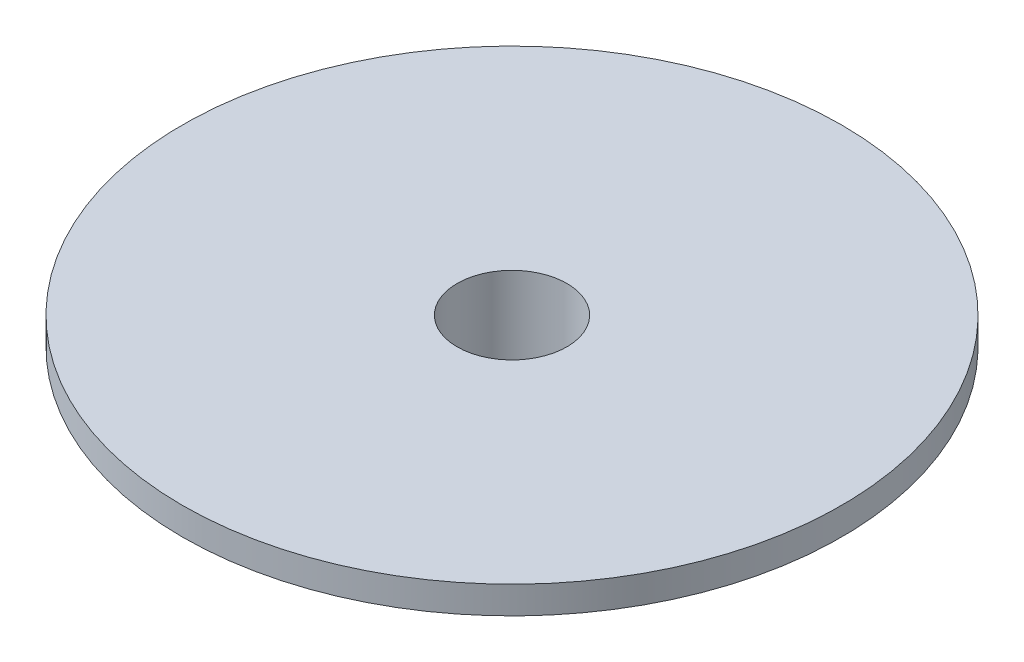
SolidWorks part; units mm, degrees
ref_plane "Front Plane" through (0, 0, 0) normal (0, 0, 1) x (1, 0, 0)
ref_plane "Top Plane" through (0, 0, 0) normal (0, 1, 0) x (1, 0, 0)
ref_plane "Right Plane" through (0, 0, 0) normal (1, 0, 0) x (0, 0, -1)
sketch "Sketch1" plane through (0, 0, 0) normal (0, 1, 0) x (1, 0, 0)
  line L1 (3.8595, 2.2639) -> (-0.0309, 4.4744)
  line L2 (-0.0309, 4.4744) -> (-3.8904, 2.2104)
  line L3 (-3.8904, 2.2104) -> (-3.8595, -2.2639)
  line L4 (-3.8595, -2.2639) -> (0.0309, -4.4744)
  line L5 (0.0309, -4.4744) -> (3.8904, -2.2104)
  line L6 (3.8904, -2.2104) -> (3.8595, 2.2639)
  circle A0 centre (0, 0) radius 3.875 construction
  circle A1 centre (0, 0) radius 2
extrude "Extrude1" add sketch "Sketch1" along normal blind 3.125
sketch "Esboço1" plane through (0, 3.125, 0) normal (0, 1, 0) x (1, 0, 0)
  circle A0 centre (0, 0) radius 12
  circle A1 centre (0, 0) radius 2
extrude "Ressalto-extrusão1" add sketch "Esboço1" along normal blind 1
fillet "Filete1" radius 1 6 edges at (-1.9143, 3.125, 3.3691) (-3.8749, 3.125, 0.0268) (-1.9606, 3.125, -3.3424) (1.9143, 3.125, -3.3691) (3.8749, 3.125, -0.0268) (1.9606, 3.125, 3.3424)
